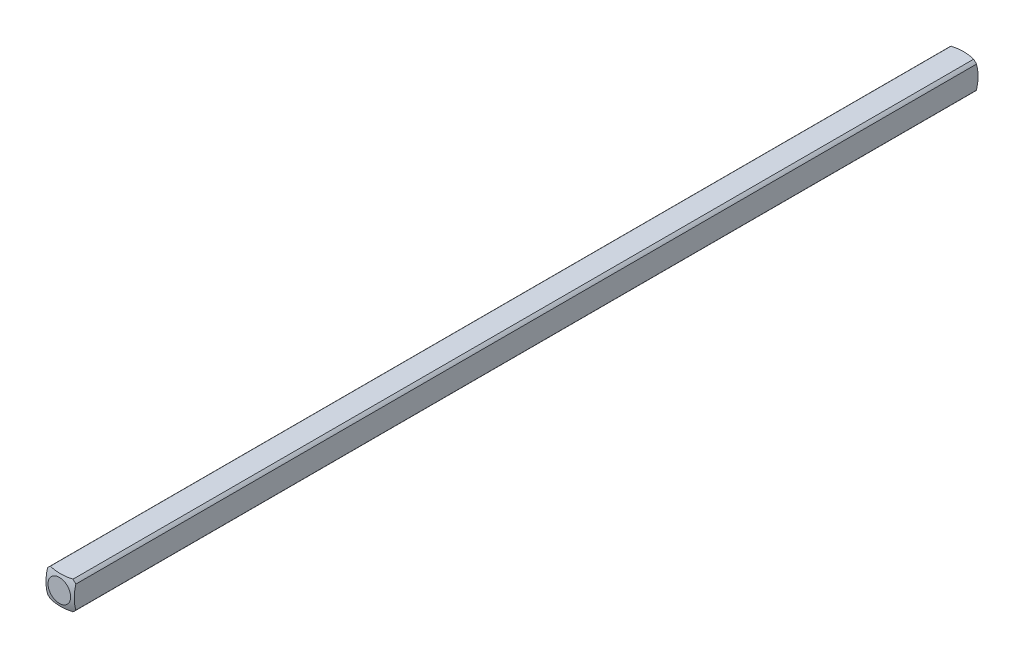
SolidWorks part; units mm, degrees
material "Custom Plastic"
ref_plane "Front Plane" through (0, 0, 0) normal (0, 0, 1) x (1, 0, 0)
ref_plane "Top Plane" through (0, 0, 0) normal (0, 1, 0) x (1, 0, 0)
ref_plane "Right Plane" through (0, 0, 0) normal (1, 0, 0) x (0, 0, -1)
sketch "Sketch1" plane through (0, 0, 0) normal (0, 0, 1) x (1, 0, 0)
  line L0 (-1.5875, -1.5875) -> (1.5875, 1.5875) construction
  line L1 (-1.5875, -1.5875) -> (1.5875, -1.5875)
  line L2 (-1.5875, -1.5875) -> (-1.5875, 1.5875)
  line L3 (-1.5875, 1.5875) -> (1.5875, 1.5875)
  line L4 (1.5875, -1.5875) -> (1.5875, 1.5875)
  dimension "D1" = 3.175
extrude "Boss-Extrude1" add sketch "Sketch1" along normal blind 50.8
sketch "Sketch2" plane through (0, 0, 0) normal (0, 0, -1) x (-1, 0, 0)
  circle A0 centre (0, 0) radius 2.032
  dimension "D1" = 4.064
extrude "Cut-Extrude1" cut sketch "Sketch2" against normal through all flip side to cut
ref_axis "Axis1" through (0, 0, 50.8) along (0, 0, -1)
sketch "Sketch3" plane through (0, 0, 0) normal (0, 1, 0) x (1, 0, 0)
  line L1 (-5.0537, -4.4027) -> (-5.0537, 5.7405)
  line L2 (-5.0537, 5.7405) -> (0, 5.7405)
  line L5 (0, -50.8) -> (0, 0) construction
  line L8 (0, 0.1609) -> (0, 5.7405)
  arc A0 (-5.0537, -4.4027) -> (0, 0.1609) centre (0, -4.9191) cw
  dimension "D1" = 5.08
revolve "Cut-Revolve1" cut sketch "Sketch3" angle 360 about axis through (0, 0, 50.8) along (0, 0, -1)
mirror "Mirror1" about plane through (0, 0, 50.8) normal (0, 0, -1) of bodies 103
